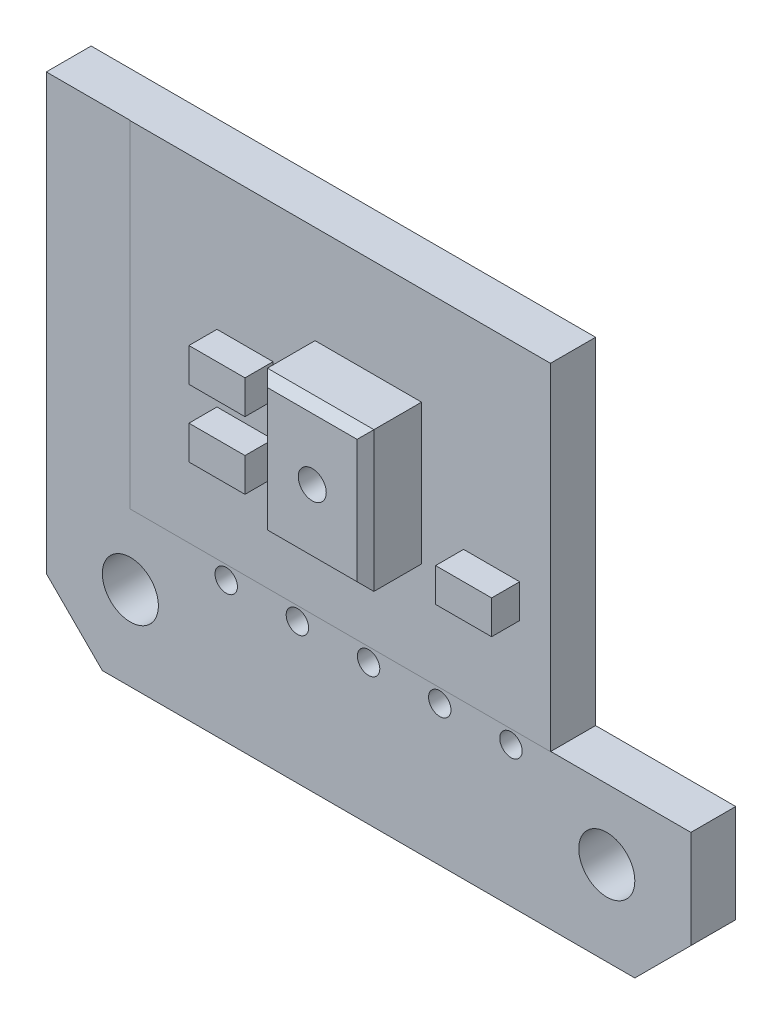
SolidWorks part; units mm, degrees
ref_plane "Front Plane" through (0, 0, 0) normal (0, 0, 1) x (1, 0, 0)
ref_plane "Top Plane" through (0, 0, 0) normal (0, 1, 0) x (1, 0, 0)
ref_plane "Right Plane" through (0, 0, 0) normal (1, 0, 0) x (0, 0, -1)
sketch "Sketch1" plane through (0, 0, 0) normal (0, 0, 1) x (1, 0, 0)
  line L0 (-11.5, 9.5) -> (-9.5, 11.5)
  line L1 (-9.5, -11.5) -> (9.5, -11.5)
  line L2 (-11.5, -9.5) -> (-11.5, 9.5)
  line L3 (-9.5, 11.5) -> (9.5, 11.5)
  line L4 (11.5, -9.5) -> (11.5, 9.5)
  line L7 (9.5, 11.5) -> (11.5, 9.5)
  line L8 (9.5, -11.5) -> (11.5, -9.5)
  line L9 (-11.5, -9.5) -> (-9.5, -11.5)
  line L11 (-9, -6) -> (9, -6) construction
  line L12 (-9, -6) -> (-9, 6) construction
  line L13 (-9, 6) -> (9, 6) construction
  line L14 (9, -6) -> (9, 6) construction
  point P0 (0, 0)
  point P1 (0, 11.5)
  point P4 (0, -6)
  point P14 (9, 0)
  point P22 (0, 0)
  dimension "D1" = 23
  dimension "D2" = 23
  dimension "D3" = 2
  dimension "D5" = 2
  dimension "D6" = 11.5
  dimension "D7" = 12
  dimension "D8" = 2.5
extrude "Boss-Extrude1" add sketch "Sketch1" along normal blind 1.6
sketch "Sketch2" plane through (0, 0, 0) normal (0, 0, 1) x (1, 0, 0)
  line L0 (11.5, -9.5) -> (11.5, 9.5) construction
  line L1 (-8.5, -6) -> (8.5, -6)
  line L2 (-8.5, -6) -> (-8.5, 6)
  line L3 (-8.5, 6) -> (8.5, 6)
  line L4 (8.5, -6) -> (8.5, 6)
  line L5 (-8.5, -6) -> (8.5, 6) construction
  line L6 (-8.5, 6) -> (8.5, -6) construction
  line L7 (-9.5, -11.5) -> (9.5, -11.5) construction
  point P0 (0, 0)
  dimension "D1" = 3
  dimension "D2" = 5.5
extrude "Boss-Extrude2" add sketch "Sketch2" along normal blind 1.61
sketch "Sketch3" plane through (0, 0, 0) normal (0, 0, 1) x (1, 0, 0)
  line L0 (0, -5.3) -> (0, -7.7) construction
  line L1 (-7, -7.7) -> (7, -7.7)
  line L2 (-7, -7.7) -> (-7, -5.3)
  line L3 (-7, -5.3) -> (7, -5.3)
  line L4 (7, -7.7) -> (7, -5.3)
  line L5 (-7, -7.7) -> (7, -5.3) construction
  line L6 (-7, -5.3) -> (7, -7.7) construction
  line L7 (-6.8, -5.5) -> (6.8, -5.5)
  line L8 (6.8, -7.5) -> (6.8, -5.5)
  line L9 (-6.8, -7.5) -> (6.8, -7.5)
  line L10 (-6.8, -7.5) -> (-6.8, -5.5)
  circle A0 centre (0, -6.5) radius 0.6
  circle A1 centre (2.54, -6.5) radius 0.6
  circle A2 centre (5.08, -6.5) radius 0.6
  circle A3 centre (-5.08, -6.5) radius 0.6
  circle A4 centre (-2.54, -6.5) radius 0.6
  circle A5 centre (-5.08, -6.5) radius 0.4
  circle A6 centre (-2.54, -6.5) radius 0.4
  circle A7 centre (0, -6.5) radius 0.4
  circle A8 centre (2.54, -6.5) radius 0.4
  circle A9 centre (5.08, -6.5) radius 0.4
  point P0 (0, -6.5)
  dimension "D6" = 1.2
  dimension "D1" = 14
  dimension "D2" = 2.4
  dimension "D3" = 6.5
  dimension "D4" = 2.54
  dimension "D5" = 2.54
  dimension "D7" = 0.2
extrude "Cut-Extrude1" cut sketch "Sketch3" along normal blind 2.62 contours A5 | A6 | A7 | A8 | A9
sketch "Sketch4" plane through (0, 0, 0) normal (0, 0, 1) x (1, 0, 0)
  line L1 (-1.9, -2.5) -> (1.9, -2.5)
  line L2 (-1.9, -2.5) -> (-1.9, 2.5)
  line L3 (-1.9, 2.5) -> (1.9, 2.5)
  line L4 (1.9, -2.5) -> (1.9, 2.5)
  line L5 (-1.9, -2.5) -> (1.9, 2.5) construction
  line L6 (-1.9, 2.5) -> (1.9, -2.5) construction
  point P0 (0, 0)
  dimension "D1" = 5
  dimension "D2" = 3.8
extrude "Boss-Extrude4" add sketch "Sketch4" along normal blind 2 from surface at 1.61 starting at face at (0, 0, 1.61)
sketch "Sketch5" plane through (0, 0, 0) normal (0, 0, 1) x (1, 0, 0)
  line L1 (-5.4, -1.3) -> (-3.4, -1.3)
  line L2 (-5.4, -1.3) -> (-5.4, -2.5)
  line L3 (-5.4, -2.5) -> (-3.4, -2.5)
  line L4 (-3.4, -1.3) -> (-3.4, -2.5)
  line L5 (-5.4, -1.3) -> (-3.4, -2.5) construction
  line L6 (-5.4, -2.5) -> (-3.4, -1.3) construction
  line L7 (-5.4, 1.1) -> (-3.4, 1.1)
  line L8 (-5.4, 1.1) -> (-5.4, -0.1)
  line L9 (-5.4, -0.1) -> (-3.4, -0.1)
  line L10 (-3.4, 1.1) -> (-3.4, -0.1)
  line L11 (-5.4, 1.1) -> (-3.4, -0.1) construction
  line L12 (-5.4, -0.1) -> (-3.4, 1.1) construction
  line L13 (3.4, -1.3) -> (5.4, -1.3)
  line L14 (3.4, -1.3) -> (3.4, -2.5)
  line L15 (3.4, -2.5) -> (5.4, -2.5)
  line L16 (5.4, -1.3) -> (5.4, -2.5)
  line L17 (3.4, -1.3) -> (5.4, -2.5) construction
  line L18 (3.4, -2.5) -> (5.4, -1.3) construction
  line L19 (1.9, -2.5) -> (1.9, 2.5) construction
  line L20 (-1.9, 2.5) -> (-1.9, -2.5) construction
  line L21 (-1.9, -2.5) -> (1.9, -2.5) construction
  point P0 (-4.4, -1.9)
  point P5 (-4.4, 0.5)
  point P10 (4.4, -1.9)
  dimension "D1" = 1.2
  dimension "D2" = 2
  dimension "D3" = 1.5
  dimension "D4" = 1.5
  dimension "D5" = 1.2
extrude "Boss-Extrude5" add sketch "Sketch5" along normal blind 1 from surface at 1.61 starting at face at (0, 0, 1.61)
chamfer "Chamfer1" distance 0.3 angle 45 4 edges at (0, -2.5, 3.61) (-1.9, 0, 3.61) (0, 2.5, 3.61) (1.9, 0, 3.61)
sketch "Sketch8" plane through (0, 0, 0) normal (0, 0, 1) x (1, 0, 0)
  line L1 (8.5, 8.5) -> (-8.5, 8.5) construction
  line L2 (8.5, 8.5) -> (8.5, -8.5) construction
  line L3 (8.5, -8.5) -> (-8.5, -8.5) construction
  line L4 (-8.5, 8.5) -> (-8.5, -8.5) construction
  line L5 (8.5, 8.5) -> (-8.5, -8.5) construction
  line L6 (8.5, -8.5) -> (-8.5, 8.5) construction
  circle A0 centre (8.5, -8.5) radius 1
  circle A1 centre (-8.5, -8.5) radius 1
  circle A2 centre (8.5, 8.5) radius 1
  circle A3 centre (-8.5, 8.5) radius 1
  point P0 (0, 0)
  dimension "D3" = 2
  dimension "D1" = 17
  dimension "D2" = 17
extrude "Cut-Extrude2" cut sketch "Sketch8" against normal mid plane 7
sketch "Sketch9" plane through (0, 0, 0) normal (0, 0, 1) x (1, 0, 0)
  line L0 (11.5, -9.5) -> (11.5, 9.5) construction
  line L1 (11.5, 6) -> (-11.5, 6)
  line L2 (11.5, 6) -> (11.5, 11.5)
  line L3 (11.5, 11.5) -> (-11.5, 11.5)
  line L4 (-11.5, 6) -> (-11.5, 11.5)
  line L5 (-11.5, 9.5) -> (-11.5, -9.5) construction
  line L6 (-8.5, 6) -> (8.5, 6) construction
  line L7 (9.5, 11.5) -> (-9.5, 11.5) construction
extrude "Cut-Extrude3" cut sketch "Sketch9" against normal mid plane 7
sketch "Sketch10" plane through (0, 0, 0) normal (0, 0, 1) x (1, 0, 0)
  line L0 (-8.5, -6) -> (8.5, -6) construction
  line L1 (11.5, 6) -> (6.5, 6)
  line L2 (11.5, 6) -> (11.5, -6)
  line L3 (11.5, -6) -> (6.5, -6)
  line L4 (6.5, 6) -> (6.5, -6)
  dimension "D1" = 5
extrude "Cut-Extrude4" cut sketch "Sketch10" against normal mid plane 7
sketch "Sketch11" plane through (0, 0, 0) normal (0, 0, 1) x (1, 0, 0)
  circle A0 centre (0, 0) radius 0.5
  dimension "D1" = 1
extrude "Cut-Extrude5" cut sketch "Sketch11" against normal blind 5 from surface at 3.61 starting at face at (0, 0, 3.61)
